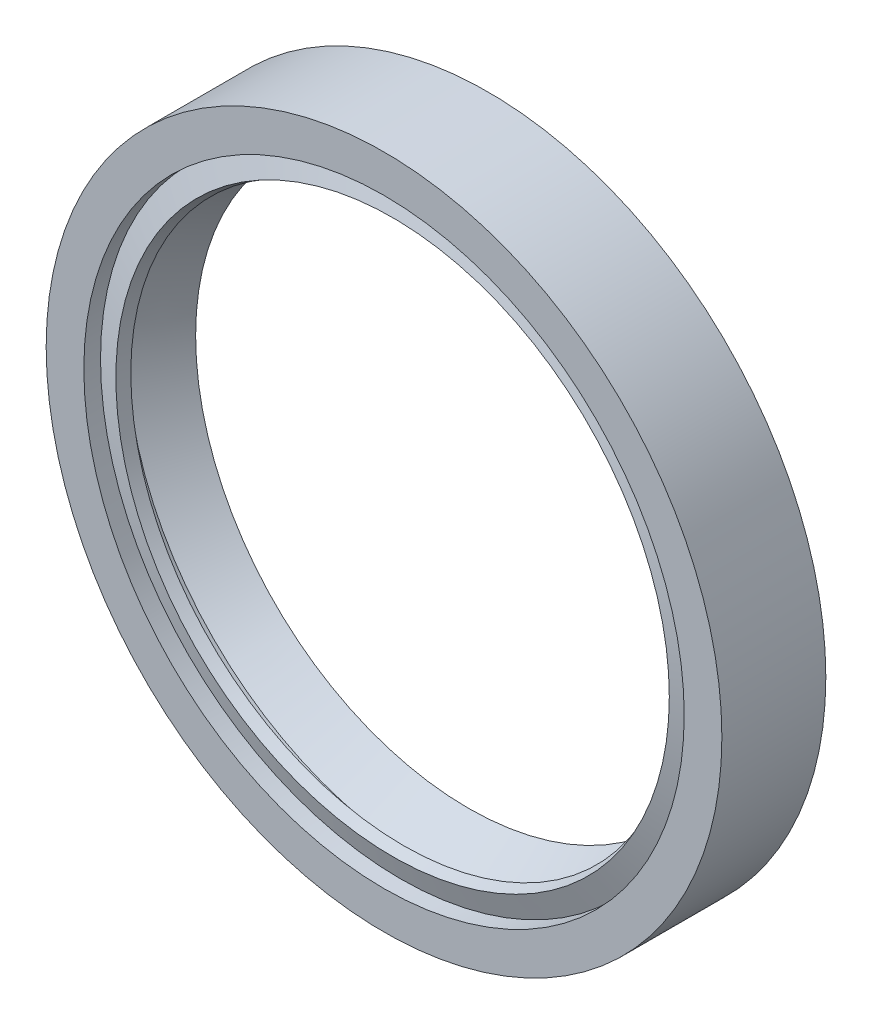
SolidWorks part; units mm, degrees
material "NBR"
ref_plane "Front Plane" through (0, 0, 0) normal (0, 0, 1) x (1, 0, 0)
ref_plane "Top Plane" through (0, 0, 0) normal (0, 1, 0) x (1, 0, 0)
ref_plane "Right Plane" through (0, 0, 0) normal (1, 0, 0) x (0, 0, -1)
sketch "Sketch1" plane through (0, 0, 0) normal (1, 0, 0) x (0, 0, -1)
  line L0 (8, 26) -> (0, 26)
  line L1 (0, 26) -> (0, 23.1012)
  line L2 (0, 23.1012) -> (1.2839, 23.1012)
  line L3 (1.2839, 23.1012) -> (0.6585, 21.2959)
  line L4 (0.6585, 21.2959) -> (1.5127, 21)
  line L5 (1.5127, 21) -> (2.2407, 23.1012)
  line L6 (2.2407, 23.1012) -> (3.2672, 23.1012)
  line L7 (8, 23.1629) -> (8, 24.2561)
  line L8 (8, 24.2561) -> (1.7511, 24.2561)
  line L9 (1.7511, 24.2561) -> (1.7511, 25.1877)
  line L10 (1.7511, 25.1877) -> (8, 25.1877)
  line L11 (8, 25.1877) -> (8, 26)
  line L12 (3.2672, 23.1012) -> (6.5018, 21)
  line L13 (6.5018, 21) -> (8, 23.1629)
  line L14 (0, 0) -> (11.2863, 0) construction
  dimension "D1" = 26
  dimension "D2" = 8
  dimension "D3" = 21
revolve "Revolve1" add sketch "Sketch1" angle 360 about L14
